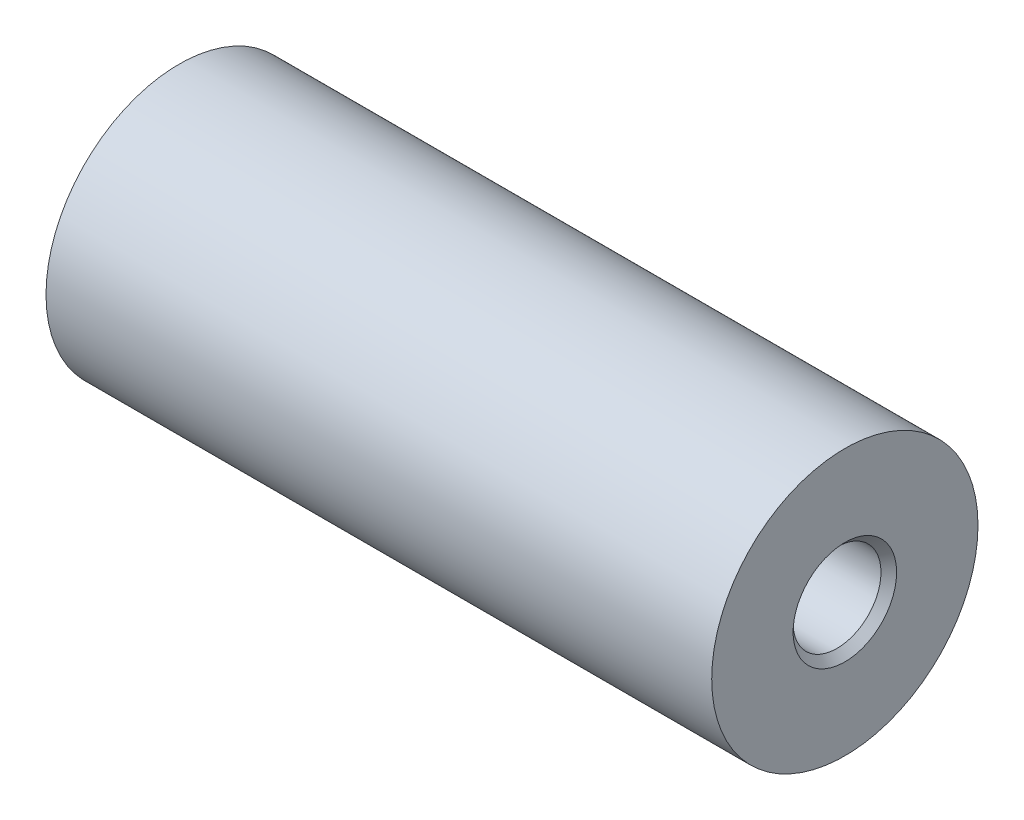
SolidWorks part; units mm, degrees
ref_plane "前视基准面" through (0, 0, 0) normal (0, 0, 1) x (1, 0, 0)
ref_plane "上视基准面" through (0, 0, 0) normal (0, 1, 0) x (1, 0, 0)
ref_plane "右视基准面" through (0, 0, 0) normal (1, 0, 0) x (0, 0, -1)
sketch "草图1" plane through (0, 0, 0) normal (1, 0, 0) x (0, 0, -1)
  circle A0 centre (0, 0) radius 10
extrude "凸台-拉伸1" add sketch "草图1" along normal blind 50
hole_wizard "G1/16 螺纹孔2" positions "草图4" profile "草图5" tap size "G1/16" standard "GB"
sketch "草图4" plane through (50, 0, 0) normal (1, 0, 0) x (0, 0, -1)
  point P0 (0, 0)
sketch "草图5" plane through (50, 0, 0) normal (0, 1, 0) x (0, 0, -1)
  line L0 (0, 0) -> (0, 51.9828)
  line L1 (0, 51.9828) -> (3.3, 50)
  line L2 (3.3, 50) -> (3.3, 0.5865)
  line L3 (3.3, 0.5865) -> (3.8865, 0)
  line L5 (3.8865, 0) -> (0, 0)
  line L6 (-3.3, 0.5865) -> (-3.8865, 0) construction
  line L10 (0, 51.9828) -> (-3.3, 50) construction
  line L11 (0, -6.35) -> (0, 107.95) construction
  dimension "螺纹孔钻头直径" = 6.6
  dimension "螺纹孔钻头深度" = 50
  dimension "近端锥形沉头孔直径" = 7.773
  dimension "近端锥形沉头孔角度" = 90
  dimension "导头角度" = 118
cosmetic thread "孔螺蚊线2"
